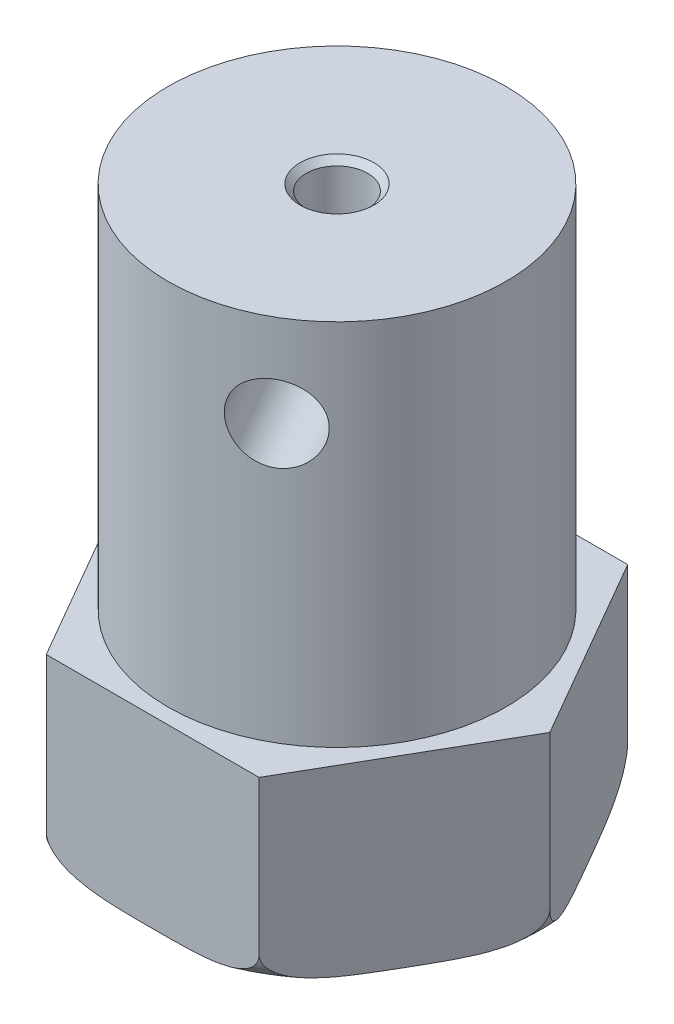
SolidWorks part; units mm, degrees
material "Chrome Stainless Steel"
ref_plane "Front Plane" through (0, 0, 0) normal (0, 0, 1) x (1, 0, 0)
ref_plane "Top Plane" through (0, 0, 0) normal (0, 1, 0) x (1, 0, 0)
ref_plane "Right Plane" through (0, 0, 0) normal (1, 0, 0) x (0, 0, -1)
sketch "Sketch1" plane through (0, 0, 0) normal (0, 1, 0) x (1, 0, 0)
  line L1 (3.4641, -6) -> (6.9282, 0)
  line L2 (6.9282, 0) -> (3.4641, 6)
  line L3 (3.4641, 6) -> (-3.4641, 6)
  line L4 (-3.4641, 6) -> (-6.9282, 0)
  line L5 (-6.9282, 0) -> (-3.4641, -6)
  line L6 (-3.4641, -6) -> (3.4641, -6)
  circle A0 centre (0, 0) radius 6 construction
  circle A1 centre (0, 0) radius 2
  dimension "D2" = 4
  dimension "D1" = 12
extrude "BASE" add sketch "Sketch1" along normal blind 6
cosmetic thread "装饰螺纹线2" [suppressed] parameters "D2"=12
sketch "Sketch2" plane through (0, 6, 0) normal (0, 1, 0) x (1, 0, 0)
  line L1 (0, 5.5) -> (0, 6) construction
  line L2 (3.4641, 6) -> (-3.4641, 6) construction
  circle A0 centre (0, 0) radius 5.5
  dimension "D1" = 0.5
  dimension "D2" = 11
extrude "SHAFT HOLDING BODY" add sketch "Sketch2" along normal blind 12
ref_plane "SET SCREW REFERENCE PLANE" through (2.75, 6, 4.7631) normal (0.5, 0, 0.866) x (0.866, 0, -0.5)
ref_axis "基准轴2" [suppressed] through (0, 22.1069, 0) along (0, -1, 0)
hole_wizard "M3x0.5 螺纹孔1" positions "Sketch7" profile "Sketch8" tap size "M3x0.5" standard "ANSI Metric" end condition through all
sketch "Sketch7" plane through (2.75, 6, 4.7631) normal (0.5, 0, 0.866) x (0.866, 0, -0.5)
  line L0 (5.5, 12) -> (-5.5, 12) construction
  line L1 (0, 12) -> (0, 0) construction
  line L2 (0, 12) -> (0, 9) construction
  point P0 (0, 9)
  dimension "D1" = 3
sketch "Sketch8" plane through (2.75, 15, 4.7631) normal (0, 1, 0) x (0.866, 0, -0.5)
  line L0 (0, 0) -> (0, 14.1603)
  line L1 (0, 14.1603) -> (1.25, 14.1603)
  line L2 (1.25, 14.1603) -> (1.25, 0)
  line L5 (1.25, 0) -> (0, 0)
  line L11 (0, -6.35) -> (0, 107.95) construction
  dimension "Thru Tap Drill Dia." = 2.5
  dimension "Thru Tap Drill Depth" = 14.1603
cosmetic thread "孔螺蚊线1" [suppressed] parameters "D2"=3
sketch "Sketch9" plane through (0, 0, 0) normal (0, 0, 1) x (1, 0, 0)
  line L0 (-6.9282, 1) -> (-6.9282, 0)
  line L1 (-6.9282, 0) -> (-5.9282, 0)
  line L2 (6, 0) -> (-6, 0) construction
  line L4 (-6.9282, 6) -> (-6.9282, 0) construction
  arc A0 (-6.9282, 1) -> (-5.9282, 0) centre (-5.9282, 1) ccw
  dimension "D1" = 1
revolve "BASE CHAMFER RELIEF" cut sketch "Sketch9" angle 360 about axis through (0, 22.1069, 0) along (0, -1, 0)
sketch "Sketch13" plane through (0, 18, 0) normal (0, 1, 0) x (1, 0, 0)
  circle A1 centre (0, 0) radius 1
  dimension "D1" = 2
extrude "SHAFT HOLE" cut sketch "Sketch13" against normal through all
chamfer "SH C" distance 0.2 angle 45 1 edges at (0, 18, 1)
